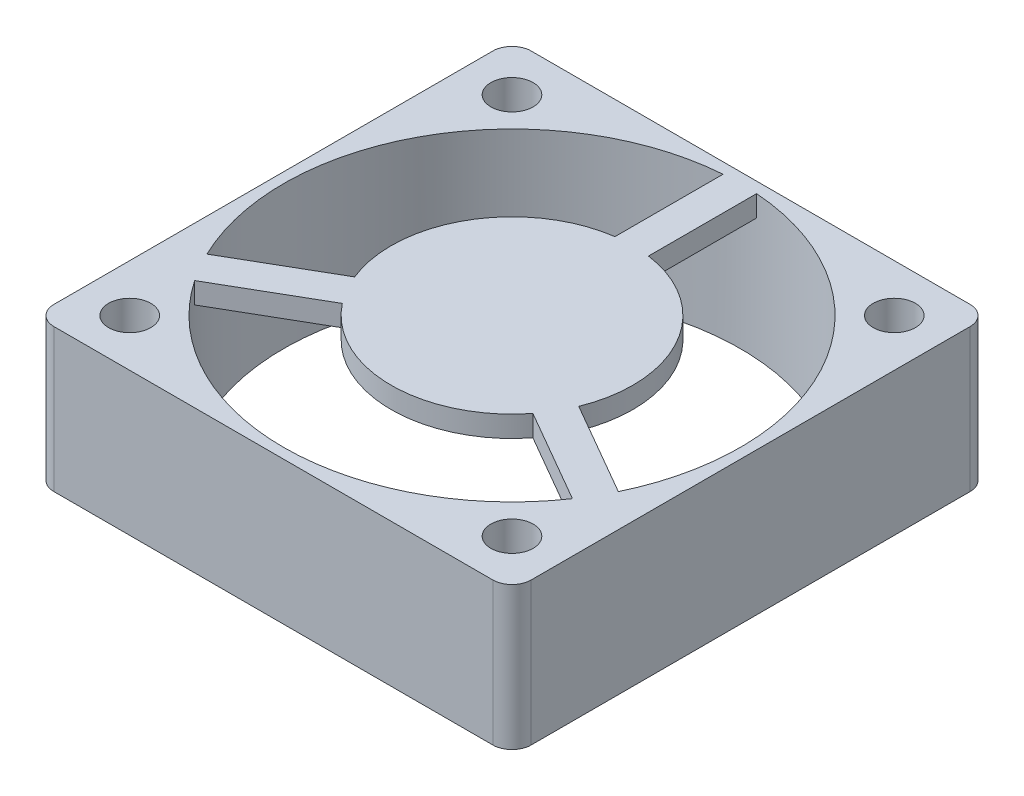
SolidWorks part; units mm, degrees
ref_plane "Front Plane" through (0, 0, 0) normal (0, 0, 1) x (1, 0, 0)
ref_plane "Top Plane" through (0, 0, 0) normal (0, 1, 0) x (1, 0, 0)
ref_plane "Right Plane" through (0, 0, 0) normal (1, 0, 0) x (0, 0, -1)
sketch "Sketch1" plane through (0, 0, 0) normal (0, 1, 0) x (1, 0, 0)
  line L1 (-24.875, -24.875) -> (24.875, -24.875)
  line L2 (-24.875, -24.875) -> (-24.875, 24.875)
  line L3 (-24.875, 24.875) -> (24.875, 24.875)
  line L4 (24.875, -24.875) -> (24.875, 24.875)
  line L5 (-24.875, -24.875) -> (24.875, 24.875) construction
  line L6 (-24.875, 24.875) -> (24.875, -24.875) construction
  point P0 (0, 0)
  dimension "D1" = 49.75
extrude "Boss-Extrude1" add sketch "Sketch1" along normal blind 14.9
fillet "Fillet1" radius 2 4 edges at (-24.875, 7.45, -24.875) (24.875, 7.45, -24.875) (24.875, 7.45, 24.875) (-24.875, 7.45, 24.875)
sketch "Sketch2" plane through (0, 14.9, 0) normal (0, 1, 0) x (1, 0, 0)
  line L1 (-19.925, 19.925) -> (19.925, 19.925) construction
  line L2 (-19.925, 19.925) -> (-19.925, -19.925) construction
  line L3 (-19.925, -19.925) -> (19.925, -19.925) construction
  line L4 (19.925, 19.925) -> (19.925, -19.925) construction
  line L5 (-24.875, 22.875) -> (-24.875, -22.875) construction
  line L7 (22.875, 24.875) -> (-22.875, 24.875) construction
  line L8 (0, 0) -> (-37.3037, 0) construction
  line L9 (0, 0) -> (0, 26.0692) construction
  circle A0 centre (-19.925, 19.925) radius 2.2
  circle A1 centre (19.925, 19.925) radius 2.2
  circle A2 centre (19.925, -19.925) radius 2.2
  circle A3 centre (-19.925, -19.925) radius 2.2
  dimension "D1" = 4.4
  dimension "D2" = 2.75
  dimension "D3" = 2.75
  dimension "D4" = 39.85
extrude "Cut-Extrude1" cut sketch "Sketch2" against normal blind 14.9
sketch "Sketch3" plane through (0, 0, 0) normal (0, -1, 0) x (1, 0, 0)
  line L1 (-17.9851, 23.285) -> (-21.8649, 23.285)
  line L2 (-21.8649, 23.285) -> (-23.8048, 19.925)
  line L3 (-23.8048, 19.925) -> (-21.8649, 16.565)
  line L4 (-21.8649, 16.565) -> (-17.9851, 16.565)
  line L5 (-17.9851, 16.565) -> (-16.0452, 19.925)
  line L6 (-16.0452, 19.925) -> (-17.9851, 23.285)
  line L7 (17.9851, 23.285) -> (16.0452, 19.925)
  line L8 (16.0452, 19.925) -> (17.9851, 16.565)
  line L9 (17.9851, 16.565) -> (21.8649, 16.565)
  line L10 (21.8649, 16.565) -> (23.8048, 19.925)
  line L11 (23.8048, 19.925) -> (21.8649, 23.285)
  line L12 (21.8649, 23.285) -> (17.9851, 23.285)
  line L13 (17.9851, -16.565) -> (16.0452, -19.925)
  line L14 (16.0452, -19.925) -> (17.9851, -23.285)
  line L15 (17.9851, -23.285) -> (21.8649, -23.285)
  line L16 (21.8649, -23.285) -> (23.8048, -19.925)
  line L17 (23.8048, -19.925) -> (21.8649, -16.565)
  line L18 (21.8649, -16.565) -> (17.9851, -16.565)
  line L19 (-21.8649, -16.565) -> (-23.8048, -19.925)
  line L20 (-23.8048, -19.925) -> (-21.8649, -23.285)
  line L21 (-21.8649, -23.285) -> (-17.9851, -23.285)
  line L22 (-17.9851, -23.285) -> (-16.0452, -19.925)
  line L23 (-16.0452, -19.925) -> (-17.9851, -16.565)
  line L24 (-17.9851, -16.565) -> (-21.8649, -16.565)
  circle A0 centre (-19.925, -19.925) radius 2.2 construction
  circle A1 centre (19.925, -19.925) radius 2.2 construction
  circle A2 centre (19.925, 19.925) radius 2.2 construction
  circle A3 centre (-19.925, 19.925) radius 2.2 construction
  circle A4 centre (-19.925, -19.925) radius 2.2 construction
  circle A5 centre (19.925, -19.925) radius 2.2 construction
  circle A6 centre (19.925, 19.925) radius 2.2 construction
  circle A7 centre (-19.925, 19.925) radius 2.2 construction
  circle A8 centre (-19.925, 19.925) radius 3.36 construction
  circle A9 centre (19.925, 19.925) radius 3.36 construction
  circle A10 centre (19.925, -19.925) radius 3.36 construction
  circle A11 centre (-19.925, -19.925) radius 3.36 construction
  point P12 (-19.925, 16.565)
  dimension "D1" = 6.72
extrude "Cut-Extrude2" cut sketch "Sketch3" against normal blind 3.7
sketch "Sketch4" plane through (0, 14.9, 0) normal (0, 1, 0) x (1, 0, 0)
  circle A0 centre (0, 0) radius 23.81
  dimension "D1" = 47.62
extrude "Cut-Extrude3" cut sketch "Sketch4" against normal through all
sketch "Sketch5" plane through (0, 14.9, 0) normal (0, 1, 0) x (1, 0, 0)
  line L0 (1.75, 12.4779) -> (1.75, 23.7456)
  line L1 (-1.75, 12.4779) -> (-1.75, 23.7456)
  line L2 (-11.6812, -4.7234) -> (-21.4393, -10.3573)
  line L3 (-9.9312, -7.7545) -> (-19.6893, -13.3883)
  line L4 (9.9312, -7.7545) -> (19.6893, -13.3883)
  line L5 (21.4393, -10.3573) -> (11.6812, -4.7234)
  line L6 (0, 0) -> (0, 23.81) construction
  line L7 (0, 0) -> (-20.6201, -11.905) construction
  line L8 (0, 0) -> (20.6201, -11.905) construction
  line L9 (-16.5602, -7.5403) -> (-14.8102, -10.5714) construction
  line L10 (-1.75, 18.1117) -> (1.75, 18.1117) construction
  line L11 (16.5602, -7.5403) -> (14.8102, -10.5714) construction
  circle A0 centre (0, 0) radius 12.6
  circle A1 centre (0, 0) radius 23.81 construction
  circle M13 centre (0, 0) radius 23.81
  dimension "D1" = 25.2
  dimension "D2" = 120
  dimension "D3" = 120
  dimension "D4" = 3.5
extrude "Boss-Extrude2" add sketch "Sketch5" against normal blind 2.2 contours A0 L0 L1 M13 | A0 | A0 L2 L3 M13 | A0 L4 L5 M13
sketch "Sketch6" plane through (0, 0, 24.875) normal (0, 0, 1) x (1, 0, 0)
  line L0 (-24.875, 7.45) -> (24.875, 7.45) construction
  line L1 (-24.875, 0) -> (-24.875, 14.9) construction
  line L2 (24.875, 14.9) -> (24.875, 0) construction
  line L3 (0, 0) -> (0, 14.9) construction
  line L4 (-22.875, 14.9) -> (22.875, 14.9) construction
sketch "Sketch7" plane through (0, 14.9, 0) normal (0, 1, 0) x (1, 0, 0)
  line L0 (0, 0) -> (0, 33.0892) construction
  line L1 (-34.2817, 0) -> (40.6454, 0) construction
  line L2 (-2.75, 0) -> (2.75, 0) construction
